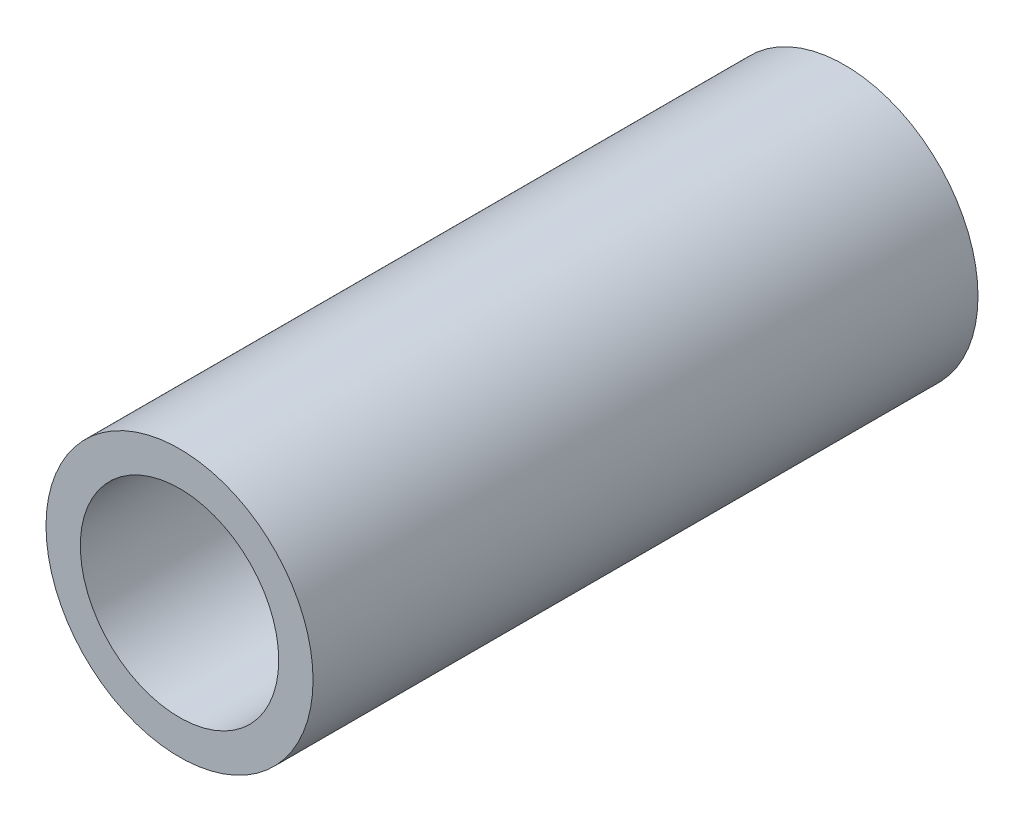
SolidWorks part; units mm, degrees
ref_plane "Front Plane" through (0, 0, 0) normal (0, 0, 1) x (1, 0, 0)
ref_plane "Top Plane" through (0, 0, 0) normal (0, 1, 0) x (1, 0, 0)
ref_plane "Right Plane" through (0, 0, 0) normal (1, 0, 0) x (0, 0, -1)
sketch "Sketch1" plane through (0, 0, 0) normal (0, 0, 1) x (1, 0, 0)
  circle A0 centre (0, 0) radius 3.1877
  circle A1 centre (0, 0) radius 2.3685
  dimension "D1" = 6.3754
  dimension "ID" = 4.7371
extrude "Extrude1" add sketch "Sketch1" along normal mid plane 15.875
sketch "Sketch2" plane through (0, 0, 0) normal (1, 0, 0) x (0, 0, -1)
  line L0 (-7.9375, -2.3685) -> (7.9375, -2.3685) construction
  line L3 (7.9375, 2.3685) -> (-7.9375, 2.3685) construction
  line L5 (-7.9375, -2.3685) -> (7.9375, -2.3685)
  line L6 (7.9375, 2.3685) -> (-7.9375, 2.3685)
sketch "Sketch4" plane through (0, 0, 7.9375) normal (0, 0, 1) x (1, 0, 0)
  line L0 (0, 0) -> (-1.6748, 1.6748)
  line L1 (0, -3.5065) -> (0, 3.5065) construction
  circle A0 centre (0, 0) radius 2.3685 construction
  dimension "D1" = 45
